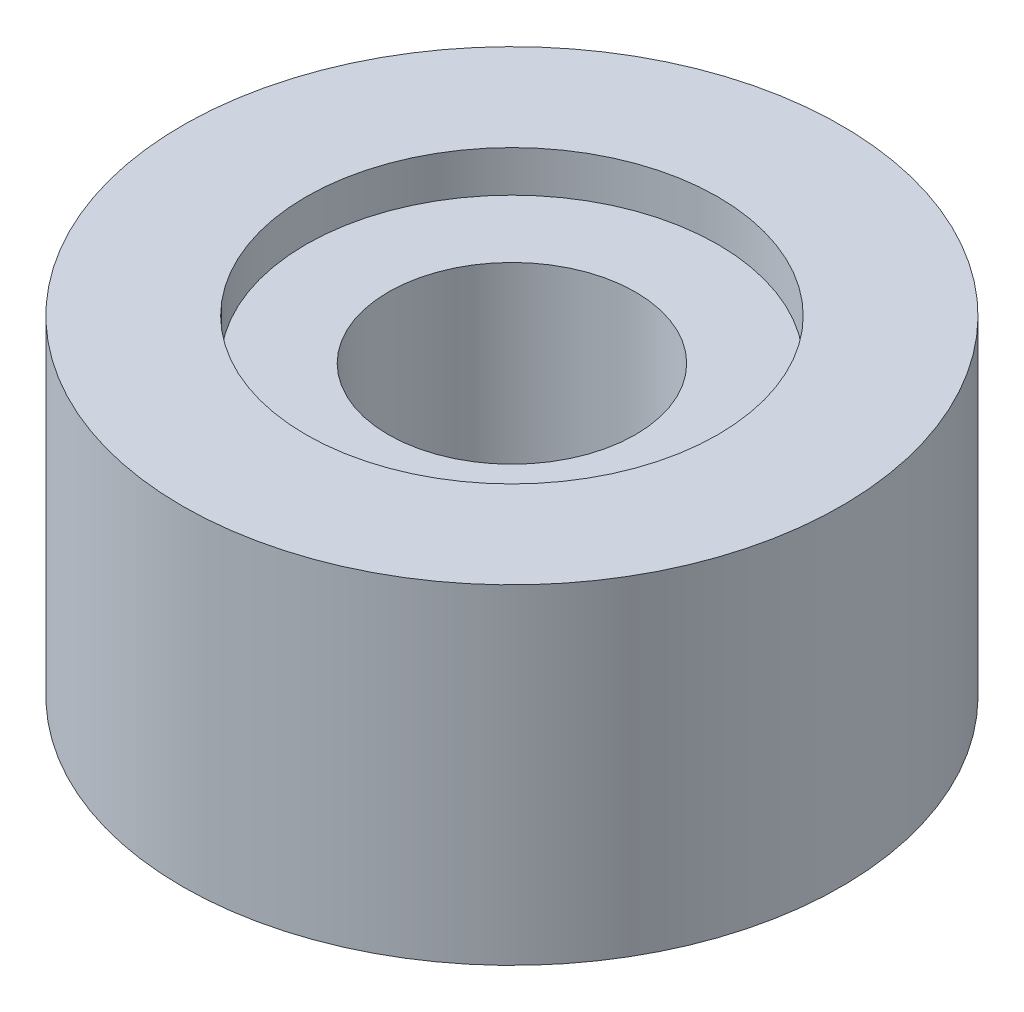
SolidWorks part; units mm, degrees
ref_plane "Plan de face" through (0, 0, 0) normal (0, 0, 1) x (1, 0, 0)
ref_plane "Plan de dessus" through (0, 0, 0) normal (0, 1, 0) x (1, 0, 0)
ref_plane "Plan de droite" through (0, 0, 0) normal (1, 0, 0) x (0, 0, -1)
sketch "Esquisse1" plane through (0, 0, 0) normal (0, 1, 0) x (1, 0, 0)
  circle A0 centre (0, 0) radius 6
  dimension "D1" = 12
extrude "Boss.-Extru.1" add sketch "Esquisse1" along normal blind 6
sketch "Esquisse2" plane through (0, 6, 0) normal (0, 1, 0) x (1, 0, 0)
  circle A0 centre (0, 0) radius 2.25
  dimension "D1" = 4.5
extrude "Enlèv. mat.-Extru.1" cut sketch "Esquisse2" against normal blind 5
sketch "Esquisse3" plane through (0, 6, 0) normal (0, 1, 0) x (1, 0, 0)
  circle A0 centre (0, 0) radius 3.75
  dimension "D1" = 7.5
extrude "Enlèv. mat.-Extru.2" cut sketch "Esquisse3" against normal blind 0.75
